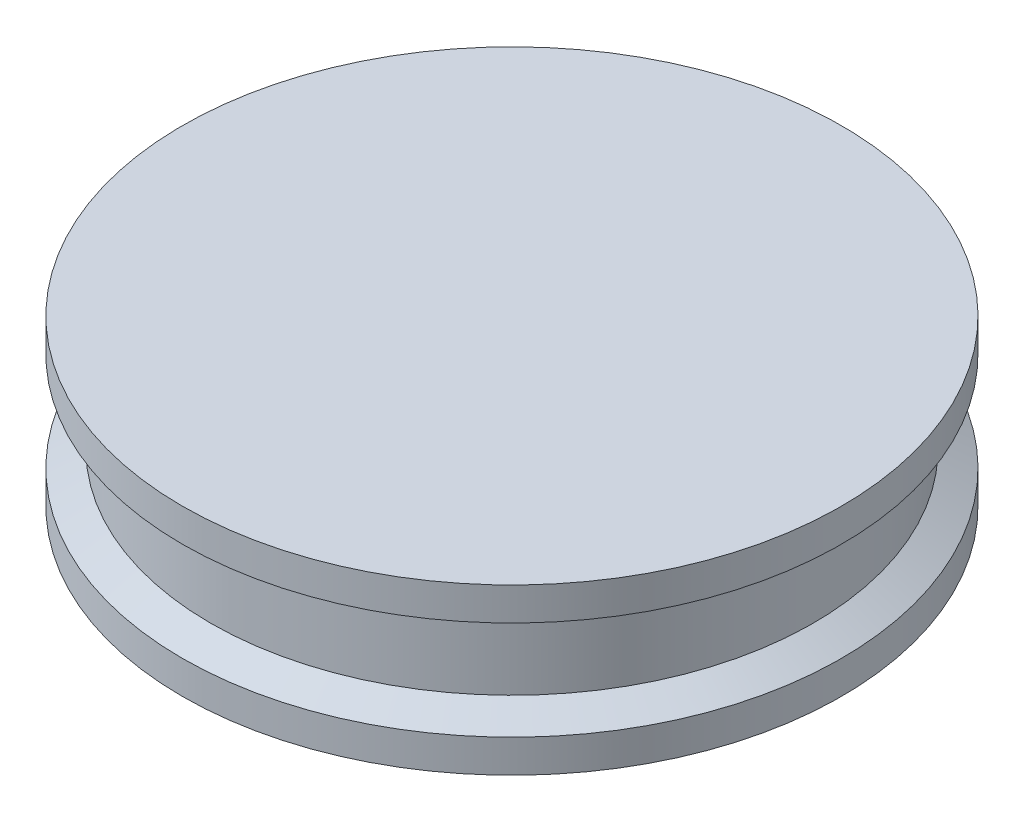
SolidWorks part; units mm, degrees
ref_plane "Front Plane" through (0, 0, 0) normal (0, 0, 1) x (1, 0, 0)
ref_plane "Top Plane" through (0, 0, 0) normal (0, 1, 0) x (1, 0, 0)
ref_plane "Right Plane" through (0, 0, 0) normal (1, 0, 0) x (0, 0, -1)
sketch "Sketch2" plane through (0, 0, 0) normal (0, 1, 0) x (1, 0, 0)
  circle A0 centre (0, 0) radius 20
  dimension "D1" = 40
extrude "Boss-Extrude1" add sketch "Sketch2" along normal mid plane 10
sketch "Sketch3" plane through (0, 0, 0) normal (1, 0, 0) x (0, 0, -1)
  line L0 (20, 3) -> (18.2845, 2.0095)
  line L1 (20, -5) -> (20, 5) construction
  line L2 (18.2845, 2.0095) -> (18.2845, -2.0095)
  line L3 (0, 0) -> (20, 0) construction
  line L4 (20, -3) -> (18.2845, -2.0095)
  line L5 (20, 3) -> (20, -3)
  line L6 (0, 7.7478) -> (0, -7.3736) construction
  point P13 (18.2845, 0)
  dimension "D1" = 120
  dimension "D2" = 2
revolve "Cut-Revolve1" cut sketch "Sketch3" angle 360 about L6
